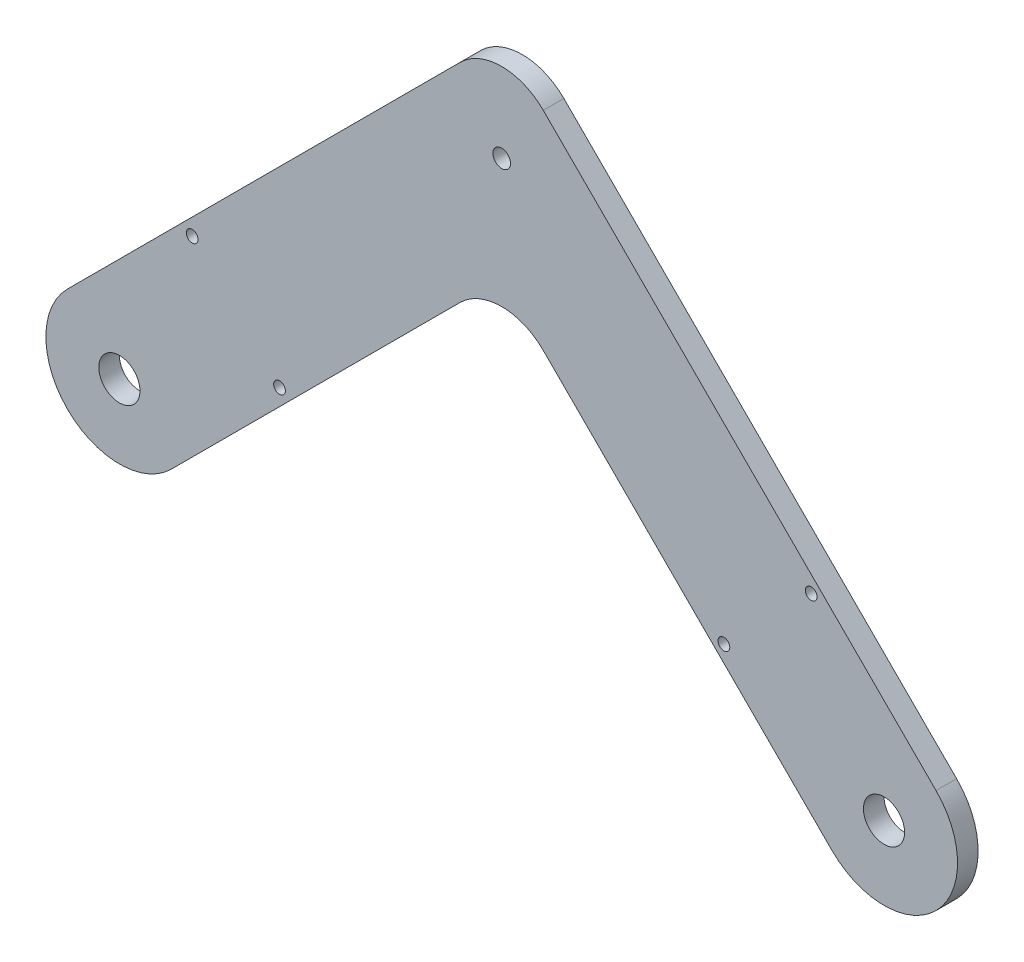
SolidWorks part; units mm, degrees
material "Acrylic (Medium-high impact)"
ref_plane "Front Plane" through (0, 0, 0) normal (0, 0, 1) x (1, 0, 0)
ref_plane "Top Plane" through (0, 0, 0) normal (0, 1, 0) x (1, 0, 0)
ref_plane "Right Plane" through (0, 0, 0) normal (1, 0, 0) x (0, 0, -1)
sketch "Sketch1" plane through (0, 0, 0) normal (0, 0, 1) x (1, 0, 0)
  line L0 (65, 0) -> (-65, 0) construction
  line L1 (-65, 0) -> (0, 65) construction
  line L2 (0, 65) -> (65, 0) construction
  line L3 (0, 65) -> (130, 65) construction
  line L4 (130, 65) -> (195, 0) construction
  circle A0 centre (-65, 0) radius 30
  circle A1 centre (65, 0) radius 30
  circle A2 centre (195, 0) radius 30
  point P4 (0, 0)
  dimension "D2" = 60
  dimension "D1" = 130
  dimension "D3" = 90
  dimension "D4" = 91.9239
  dimension "D5" = 135
  dimension "D6" = 130
sketch "Sketch2" plane through (0, 0, 0) normal (0, 0, 1) x (1, 0, 0)
  line L4 (-56.1612, -8.8388) -> (0, 47.3223)
  line L5 (0, 47.3223) -> (56.1612, -8.8388)
  line L6 (-73.8388, 8.8388) -> (0, 82.6777)
  line L7 (0, 82.6777) -> (73.8388, 8.8388)
  line L19 (56.1612, -8.8388) -> (0, 47.3223)
  circle A0 centre (-65, 0) radius 3.5
  circle A1 centre (65, 0) radius 3.5
  arc A4 (56.1612, -8.8388) -> (73.8388, 8.8388) centre (65, 0) ccw
  arc A5 (-73.8388, 8.8388) -> (-56.1612, -8.8388) centre (-65, 0) ccw
  circle A6 centre (65, 0) radius 3.5
  circle A7 centre (0, 65) radius 1.5
  point P18 (-65, 0)
  dimension "D6" = 3
  dimension "D1" = 25
  dimension "D2" = 90
extrude "Boss-Extrude1" add sketch "Sketch2" against normal blind 3.5
fillet "Fillet1" radius 10 2 edges at (0, 47.3223, -1.75) (0, 82.6777, -1.75)
sketch "Sketch3" plane through (0, 0, 0) normal (0, 0, 1) x (1, 0, 0)
  line L0 (-65, 0) -> (-45.201, 19.799) construction
  line L1 (-56.1612, -8.8388) -> (-7.0711, 40.2513) construction
  line L2 (-37.7764, 12.3744) -> (-52.6256, 27.2236) construction
  line L3 (0, 27.2236) -> (0, 12.3744) construction
  line L4 (37.7764, 12.3744) -> (52.6256, 27.2236) construction
  line L5 (65, 0) -> (45.201, 19.799) construction
  circle A0 centre (-52.6256, 27.2236) radius 1
  circle A1 centre (-37.7764, 12.3744) radius 1
  circle A2 centre (37.7764, 12.3744) radius 1
  circle A3 centre (52.6256, 27.2236) radius 1
  point P8 (-45.201, 19.799)
  dimension "D3" = 2
  dimension "D1" = 28
  dimension "D2" = 2
extrude "Cut-Extrude1" cut sketch "Sketch3" against normal blind 10
